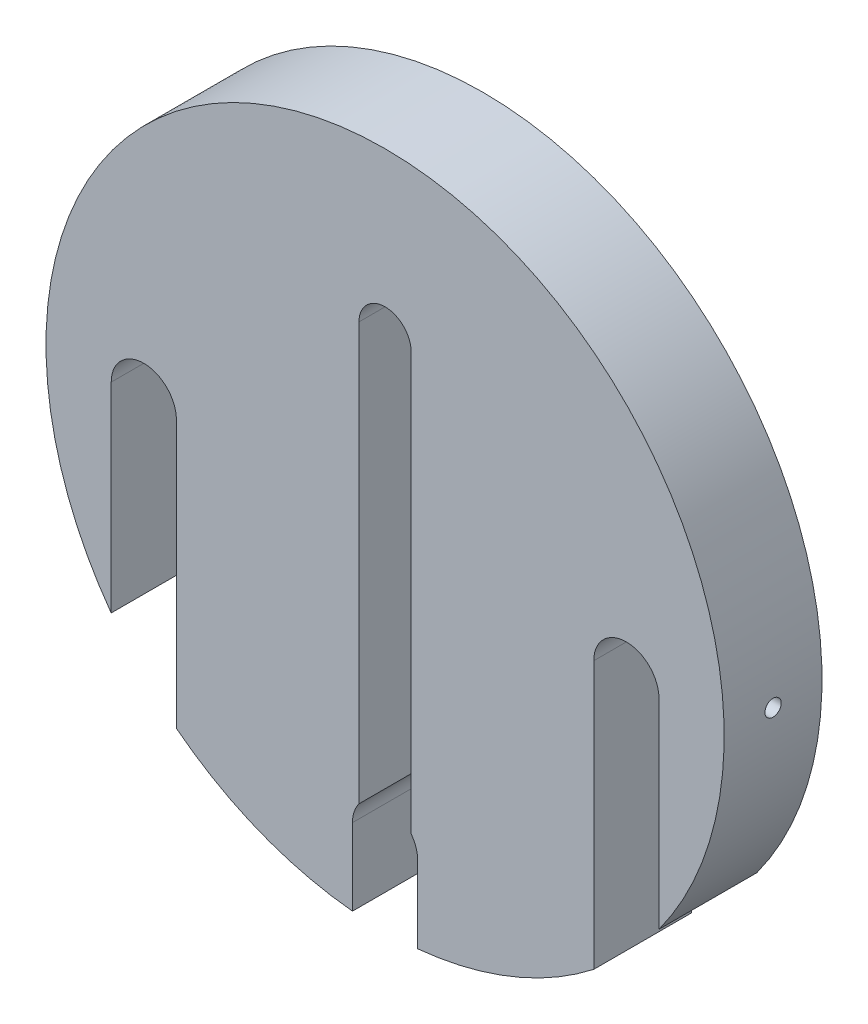
SolidWorks part; units mm, degrees
material "Malleable Cast Iron"
ref_plane "Front Plane" through (0, 0, 0) normal (0, 0, 1) x (1, 0, 0)
ref_plane "Top Plane" through (0, 0, 0) normal (0, 1, 0) x (1, 0, 0)
ref_plane "Right Plane" through (0, 0, 0) normal (1, 0, 0) x (0, 0, -1)
sketch "Sketch1" plane through (0, 0, 0) normal (0, 0, 1) x (1, 0, 0)
  circle A0 centre (0, 0) radius 52
  dimension "D1" = 104
extrude "Boss-Extrude1" add sketch "Sketch1" along normal blind 15
sketch "Sketch2" plane through (0, 0, 15) normal (0, 0, 1) x (1, 0, 0)
  line L0 (0, 0) -> (0, -16.5156) construction
  line L2 (32, 0) -> (32, -45)
  line L3 (32, -45) -> (42, -45)
  line L4 (42, 0) -> (42, -45)
  line L6 (-5, -40) -> (-5, -55)
  line L7 (-5, -55) -> (5, -55)
  line L8 (5, -40) -> (5, -55)
  line L9 (-32, -45) -> (-42, -45)
  line L10 (-42, 0) -> (-42, -45)
  line L12 (-32, 0) -> (-32, -45)
  arc A1 (32, 0) -> (42, 0) centre (37, 0) cw
  arc A2 (-32, 0) -> (-42, 0) centre (-37, 0) ccw
  arc A3 (5, -40) -> (-5, -40) centre (0, -40) ccw
  point P21 (0, 0)
  point P24 (-23.4865, -40.697)
  dimension "D9" = 5
  dimension "D3" = 5
  dimension "D2" = 5
extrude "Cut-Extrude1" cut sketch "Sketch2" against normal blind 15
sketch "Sketch3" plane through (0, 0, 15) normal (0, 0, 1) x (1, 0, 0)
  line L2 (4, 27) -> (4, -40)
  line L3 (4, -40) -> (-4, -40)
  line L4 (-4, 27) -> (-4, -40)
  arc A0 (5, -40) -> (-5, -40) centre (0, -40) ccw construction
  arc A2 (-4, 27) -> (4, 27) centre (0, 27) cw
  dimension "D6" = 4
  dimension "D3" = 0
extrude "Cut-Extrude2" cut sketch "Sketch3" against normal blind 30 contours L4 L3 L2 A2
ref_plane "Plane1" through (-52, 0, 0) normal (-1, 0, 0) x (0, 0, 1)
hole_wizard "M3 Tapped Hole1" positions "Sketch7" profile "Sketch8" tap size "M3" standard "ISO"
sketch "Sketch7" plane through (-52, 0, 0) normal (-1, 0, 0) x (0, 0, 1)
  point P0 (7.5, 0)
  dimension "D1" = 7.5
sketch "Sketch8" plane through (-52, 0, 7.5) normal (0, 1, 0) x (0, 0, 1)
  line L0 (0, 0) -> (0, 48)
  line L1 (0, 48) -> (1.25, 48)
  line L2 (1.25, 48) -> (1.25, 0)
  line L5 (1.25, 0) -> (0, 0)
  line L11 (0, -6.35) -> (0, 107.95) construction
  dimension "Thru Tap Drill Dia." = 2.5
  dimension "Thru Tap Drill Depth" = 48
cosmetic thread "Hole Thread2" parameters "D2"=3
mirror "Mirror1" about plane through (0, 0, 0) normal (1, 0, 0) of "M3 Tapped Hole1"
